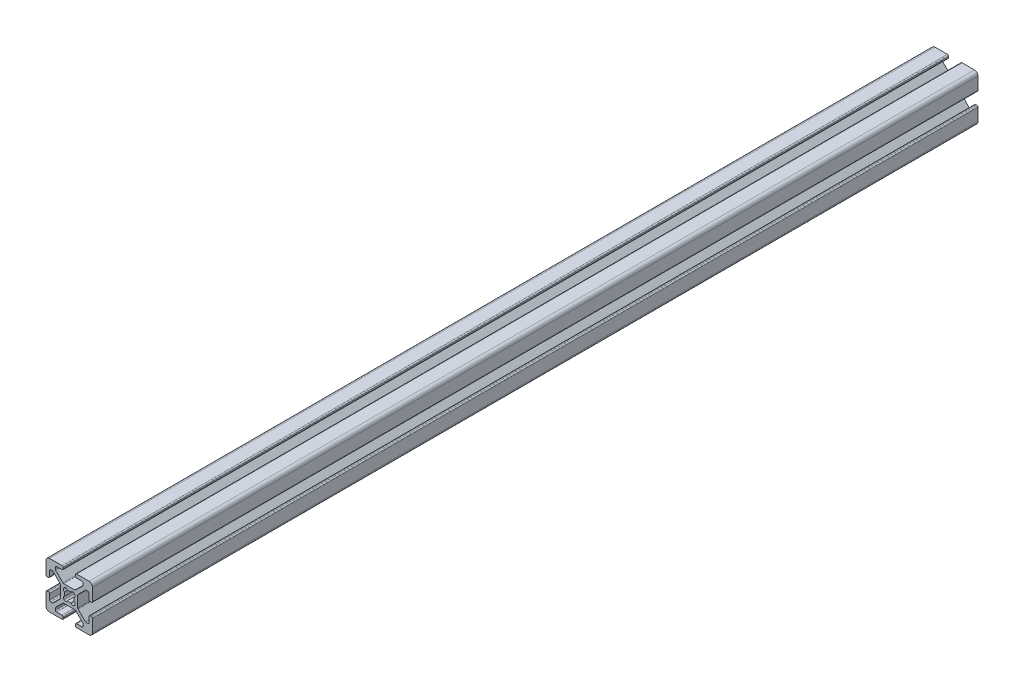
SolidWorks part; units mm, degrees
ref_plane "Front Plane" through (0, 0, 0) normal (0, 0, 1) x (1, 0, 0)
ref_plane "Top Plane" through (0, 0, 0) normal (0, 1, 0) x (1, 0, 0)
ref_plane "Right Plane" through (0, 0, 0) normal (1, 0, 0) x (0, 0, -1)
ref_plane "Plane1" through (0, 0, -457.2) normal (0, 0, -1) x (-1, 0, 0)
sketch "Sketch1" plane through (0, 0, -457.2) normal (0, 0, -1) x (-1, 0, 0)
  line L0 (2.3045, -2.1245) -> (2.1245, -2.3045)
  line L1 (-2.1245, -2.3045) -> (-2.3045, -2.1245)
  line L2 (-2.3045, 2.1245) -> (-2.1245, 2.3045)
  line L3 (2.1245, 2.3045) -> (2.3045, 2.1245)
  line L4 (10, -8.5) -> (10, -3.138)
  line L5 (9.492, -2.63) -> (9.008, -2.63)
  line L6 (8.5, -3.138) -> (8.5, -5.487)
  line L7 (7.992, -5.995) -> (7.2659, -5.995)
  line L8 (6.9067, -5.8462) -> (3.8038, -2.7433)
  line L9 (3.655, -2.3841) -> (3.655, 2.3838)
  line L10 (3.8038, 2.743) -> (6.907, 5.8462)
  line L11 (7.2662, 5.995) -> (7.992, 5.995)
  line L12 (8.5, 5.487) -> (8.5, 3.138)
  line L13 (9.008, 2.63) -> (9.492, 2.63)
  line L14 (10, 3.138) -> (10, 8.5)
  line L15 (8.5, 10) -> (3.138, 10)
  line L16 (2.63, 9.492) -> (2.63, 9.008)
  line L17 (3.138, 8.5) -> (5.487, 8.5)
  line L18 (5.995, 7.992) -> (5.995, 7.2659)
  line L19 (5.8462, 6.9067) -> (2.7433, 3.8038)
  line L20 (2.3841, 3.655) -> (-2.3838, 3.655)
  line L21 (-2.743, 3.8038) -> (-5.8462, 6.907)
  line L22 (-5.995, 7.2662) -> (-5.995, 7.992)
  line L23 (-5.487, 8.5) -> (-3.138, 8.5)
  line L24 (-2.63, 9.008) -> (-2.63, 9.492)
  line L25 (-3.138, 10) -> (-8.5, 10)
  line L26 (-10, 8.5) -> (-10, 3.138)
  line L27 (-9.492, 2.63) -> (-9.008, 2.63)
  line L28 (-8.5, 3.138) -> (-8.5, 5.487)
  line L29 (-7.992, 5.995) -> (-7.2659, 5.995)
  line L30 (-6.9067, 5.8462) -> (-3.8038, 2.7433)
  line L31 (-3.655, 2.3841) -> (-3.655, -2.3838)
  line L32 (-3.8038, -2.743) -> (-6.907, -5.8462)
  line L33 (-7.2662, -5.995) -> (-7.992, -5.995)
  line L34 (-8.5, -5.487) -> (-8.5, -3.138)
  line L35 (-9.008, -2.63) -> (-9.492, -2.63)
  line L36 (-10, -3.138) -> (-10, -8.5)
  line L37 (-8.5, -10) -> (-3.138, -10)
  line L38 (-2.63, -9.492) -> (-2.63, -9.008)
  line L39 (-3.138, -8.5) -> (-5.487, -8.5)
  line L40 (-5.995, -7.992) -> (-5.995, -7.2659)
  line L41 (-5.8462, -6.9067) -> (-2.7433, -3.8038)
  line L42 (-2.3841, -3.655) -> (2.3838, -3.655)
  line L43 (2.743, -3.8038) -> (5.8462, -6.907)
  line L44 (5.995, -7.2662) -> (5.995, -7.992)
  line L45 (5.487, -8.5) -> (3.138, -8.5)
  line L46 (2.63, -9.008) -> (2.63, -9.492)
  line L47 (3.138, -10) -> (8.5, -10)
  arc A0 (1.9358, 0.8037) -> (1.9358, -0.8037) centre (0, 0) cw
  arc A1 (1.9358, -0.8037) -> (2.3045, -2.1245) centre (1.748, -1.568) cw
  arc A2 (2.1245, -2.3045) -> (0.8037, -1.9358) centre (1.568, -1.748) cw
  arc A3 (0.8037, -1.9358) -> (-0.8037, -1.9358) centre (0, 0) cw
  arc A4 (-0.8037, -1.9358) -> (-2.1245, -2.3045) centre (-1.568, -1.748) cw
  arc A5 (-2.3045, -2.1245) -> (-1.9358, -0.8037) centre (-1.748, -1.568) cw
  arc A6 (-1.9358, -0.8037) -> (-1.9358, 0.8037) centre (0, 0) cw
  arc A7 (-1.9358, 0.8037) -> (-2.3045, 2.1245) centre (-1.748, 1.568) cw
  arc A8 (-2.1245, 2.3045) -> (-0.8037, 1.9358) centre (-1.568, 1.748) cw
  arc A9 (-0.8037, 1.9358) -> (0.8037, 1.9358) centre (0, 0) cw
  arc A10 (0.8037, 1.9358) -> (2.1245, 2.3045) centre (1.568, 1.748) cw
  arc A11 (2.3045, 2.1245) -> (1.9358, 0.8037) centre (1.748, 1.568) cw
  arc A12 (10, -3.138) -> (9.492, -2.63) centre (9.492, -3.138) ccw
  arc A13 (9.008, -2.63) -> (8.5, -3.138) centre (9.008, -3.138) ccw
  arc A14 (8.5, -5.487) -> (7.992, -5.995) centre (7.992, -5.487) cw
  arc A15 (7.2659, -5.995) -> (6.9067, -5.8462) centre (7.2659, -5.487) cw
  arc A16 (3.8038, -2.7433) -> (3.655, -2.3841) centre (4.163, -2.3841) cw
  arc A17 (3.655, 2.3838) -> (3.8038, 2.743) centre (4.163, 2.3838) cw
  arc A18 (6.907, 5.8462) -> (7.2662, 5.995) centre (7.2662, 5.487) cw
  arc A19 (7.992, 5.995) -> (8.5, 5.487) centre (7.992, 5.487) cw
  arc A20 (8.5, 3.138) -> (9.008, 2.63) centre (9.008, 3.138) ccw
  arc A21 (9.492, 2.63) -> (10, 3.138) centre (9.492, 3.138) ccw
  arc A22 (10, 8.5) -> (8.5, 10) centre (8.5, 8.5) ccw
  arc A23 (3.138, 10) -> (2.63, 9.492) centre (3.138, 9.492) ccw
  arc A24 (2.63, 9.008) -> (3.138, 8.5) centre (3.138, 9.008) ccw
  arc A25 (5.487, 8.5) -> (5.995, 7.992) centre (5.487, 7.992) cw
  arc A26 (5.995, 7.2659) -> (5.8462, 6.9067) centre (5.487, 7.2659) cw
  arc A27 (2.7433, 3.8038) -> (2.3841, 3.655) centre (2.3841, 4.163) cw
  arc A28 (-2.3838, 3.655) -> (-2.743, 3.8038) centre (-2.3838, 4.163) cw
  arc A29 (-5.8462, 6.907) -> (-5.995, 7.2662) centre (-5.487, 7.2662) cw
  arc A30 (-5.995, 7.992) -> (-5.487, 8.5) centre (-5.487, 7.992) cw
  arc A31 (-3.138, 8.5) -> (-2.63, 9.008) centre (-3.138, 9.008) ccw
  arc A32 (-2.63, 9.492) -> (-3.138, 10) centre (-3.138, 9.492) ccw
  arc A33 (-8.5, 10) -> (-10, 8.5) centre (-8.5, 8.5) ccw
  arc A34 (-10, 3.138) -> (-9.492, 2.63) centre (-9.492, 3.138) ccw
  arc A35 (-9.008, 2.63) -> (-8.5, 3.138) centre (-9.008, 3.138) ccw
  arc A36 (-8.5, 5.487) -> (-7.992, 5.995) centre (-7.992, 5.487) cw
  arc A37 (-7.2659, 5.995) -> (-6.9067, 5.8462) centre (-7.2659, 5.487) cw
  arc A38 (-3.8038, 2.7433) -> (-3.655, 2.3841) centre (-4.163, 2.3841) cw
  arc A39 (-3.655, -2.3838) -> (-3.8038, -2.743) centre (-4.163, -2.3838) cw
  arc A40 (-6.907, -5.8462) -> (-7.2662, -5.995) centre (-7.2662, -5.487) cw
  arc A41 (-7.992, -5.995) -> (-8.5, -5.487) centre (-7.992, -5.487) cw
  arc A42 (-8.5, -3.138) -> (-9.008, -2.63) centre (-9.008, -3.138) ccw
  arc A43 (-9.492, -2.63) -> (-10, -3.138) centre (-9.492, -3.138) ccw
  arc A44 (-10, -8.5) -> (-8.5, -10) centre (-8.5, -8.5) ccw
  arc A45 (-3.138, -10) -> (-2.63, -9.492) centre (-3.138, -9.492) ccw
  arc A46 (-2.63, -9.008) -> (-3.138, -8.5) centre (-3.138, -9.008) ccw
  arc A47 (-5.487, -8.5) -> (-5.995, -7.992) centre (-5.487, -7.992) cw
  arc A48 (-5.995, -7.2659) -> (-5.8462, -6.9067) centre (-5.487, -7.2659) cw
  arc A49 (-2.7433, -3.8038) -> (-2.3841, -3.655) centre (-2.3841, -4.163) cw
  arc A50 (2.3838, -3.655) -> (2.743, -3.8038) centre (2.3838, -4.163) cw
  arc A51 (5.8462, -6.907) -> (5.995, -7.2662) centre (5.487, -7.2662) cw
  arc A52 (5.995, -7.992) -> (5.487, -8.5) centre (5.487, -7.992) cw
  arc A53 (3.138, -8.5) -> (2.63, -9.008) centre (3.138, -9.008) ccw
  arc A54 (2.63, -9.492) -> (3.138, -10) centre (3.138, -9.492) ccw
  arc A55 (8.5, -10) -> (10, -8.5) centre (8.5, -8.5) ccw
extrude "Boss-Extrude1" add sketch "Sketch1" against normal blind 381
